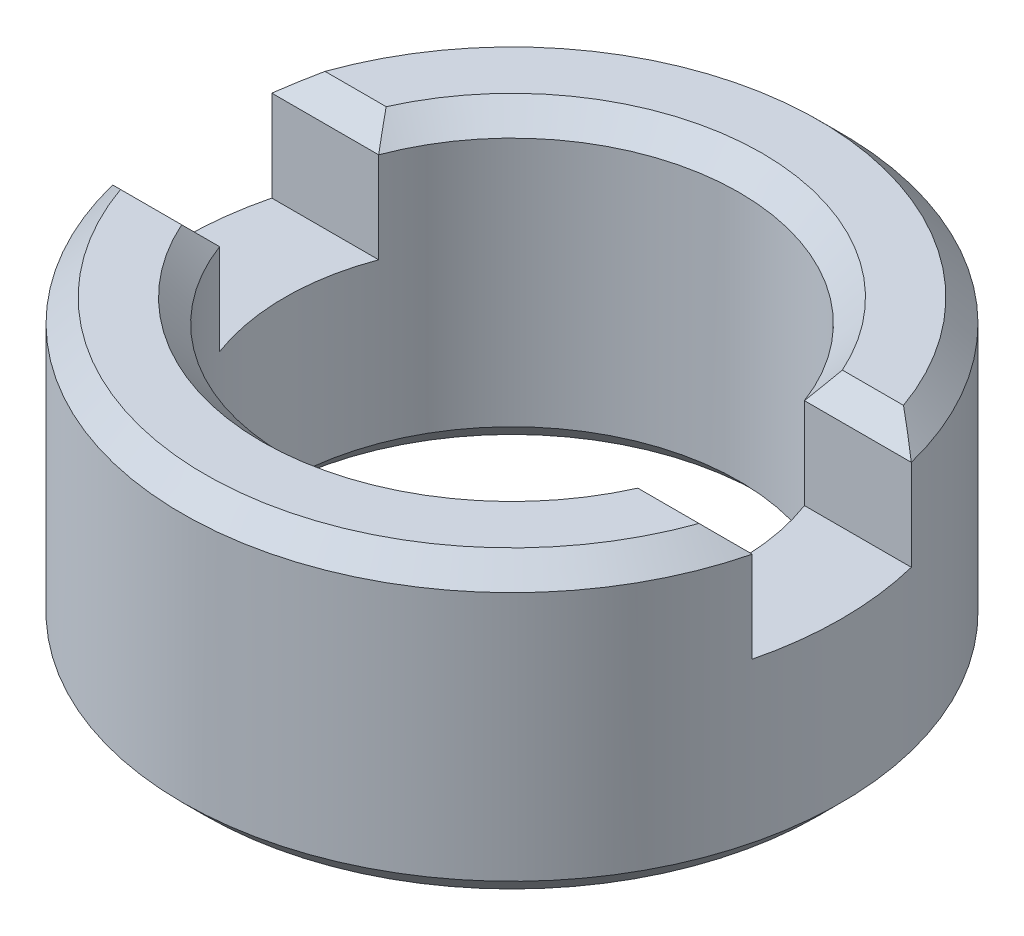
SolidWorks part; units mm, degrees
material "AISI 304"
ref_plane "Front Plane" through (0, 0, 0) normal (0, 0, 1) x (1, 0, 0)
ref_plane "Top Plane" through (0, 0, 0) normal (0, 1, 0) x (1, 0, 0)
ref_plane "Right Plane" through (0, 0, 0) normal (1, 0, 0) x (0, 0, -1)
sketch "Sketch1" plane through (0, 0, 0) normal (0, 1, 0) x (1, 0, 0)
  circle A0 centre (0, 0) radius 1.8415
  dimension "D1" = 3.683
extrude "Boss-Extrude1" add sketch "Sketch1" along normal mid plane 1.651
sketch "Sketch3" plane through (0, -0.8255, 0) normal (0, -1, 0) x (1, 0, 0)
  circle A0 centre (0, 0) radius 1.27
  dimension "D1" = 2.54
extrude "Cut-Extrude2" cut sketch "Sketch3" against normal through all
sketch "Sketch7" plane through (0, 0.8255, 0) normal (0, -1, 0) x (1, 0, 0)
  line L0 (1.1897, -0.4445) -> (1.787, -0.4445)
  line L1 (-1.787, 0.4445) -> (-1.1897, 0.4445)
  line L3 (-1.787, -0.4445) -> (-1.1897, -0.4445)
  line L5 (1.1897, 0.4445) -> (1.787, 0.4445)
  circle A0 centre (0, 0) radius 1.8415 construction
  circle A1 centre (0, 0) radius 1.27 construction
  arc A2 (1.787, -0.4445) -> (1.787, 0.4445) centre (0, 0) ccw
  arc A3 (1.1897, -0.4445) -> (1.1897, 0.4445) centre (0, 0) ccw
  arc A4 (-1.1897, 0.4445) -> (-1.1897, -0.4445) centre (0, 0) ccw
  arc A5 (-1.787, 0.4445) -> (-1.787, -0.4445) centre (0, 0) ccw
  dimension "D1" = 0.889
  dimension "D2" = 0.4445
extrude "Cut-Extrude6" cut sketch "Sketch7" along normal blind 0.635
chamfer "Chamfer1" distance 0.127 angle 45 10 edges at (0, -0.8255, -1.27) (0, -0.8255, 1.8415) (1.4884, 0.8255, -0.4445) (0, 0.8255, -1.27) (-1.4884, 0.8255, -0.4445) (0, 0.8255, -1.8415) (1.4884, 0.8255, 0.4445) (0, 0.8255, 1.27) (-1.4884, 0.8255, 0.4445) (0, 0.8255, 1.8415)
